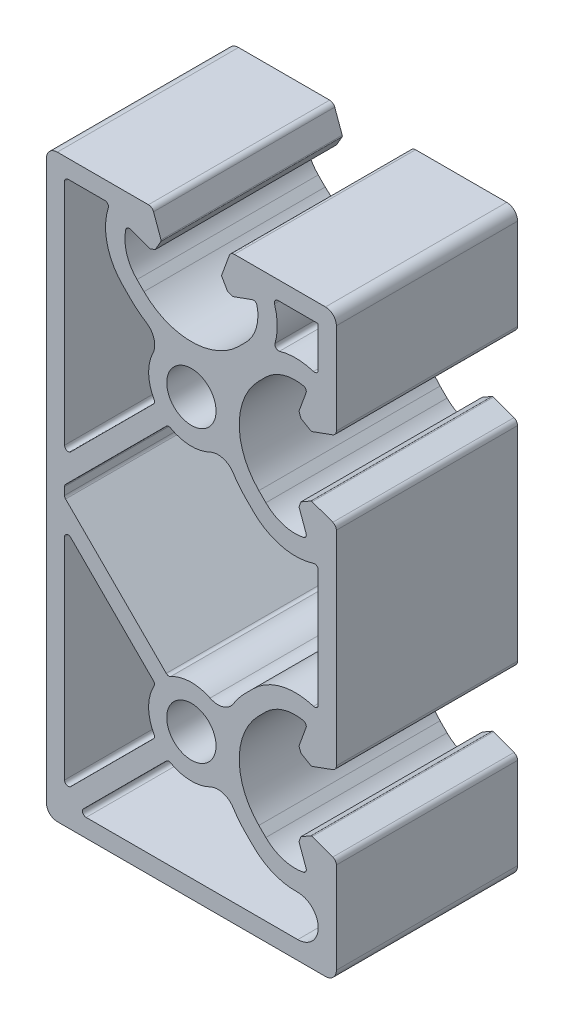
SolidWorks part; units mm, degrees
material "6005-T5"
ref_plane "Front" through (0, 0, 0) normal (0, 0, 1) x (1, 0, 0)
ref_plane "Top" through (0, 0, 0) normal (0, 1, 0) x (1, 0, 0)
ref_plane "Right" through (0, 0, 0) normal (1, 0, 0) x (0, 0, -1)
sketch "Sk Main Extrusion" plane through (0, 0, 0) normal (0, 0, 1) x (1, 0, 0)
  line L118 (-17.5, 37) -> (-17.5, 5.4749)
  line L119 (-16.6464, 5.1213) -> (-5.2369, 16.5309)
  line L120 (-8.3085, 27.4415) -> (-9.4443, 28.5773)
  line L121 (-11.9407, 37.5) -> (-17, 37.5)
  line L122 (-3.4691, 14.7631) -> (-17.3536, 0.8787)
  line L123 (-17.5, 0.5251) -> (-17.5, -0.5251)
  line L124 (-17.3536, -0.8787) -> (-3.4691, -14.7631)
  line L125 (7.4415, -11.6915) -> (8.5773, -10.5557)
  line L126 (17.5, -8.0593) -> (17.5, 8.0593)
  line L127 (8.5773, 10.5557) -> (7.4415, 11.6915)
  line L128 (-17.5, -5.4749) -> (-17.5, -34.5251)
  line L129 (-16.6464, -34.8787) -> (-5.2369, -23.4691)
  line L130 (-5.2369, -16.5309) -> (-16.6464, -5.1213)
  line L131 (-3.4691, -25.2369) -> (-14.8787, -36.6464)
  line L132 (-14.5251, -37.5) -> (14.671, -37.5)
  line L133 (8.5773, -29.4443) -> (7.4415, -28.3085)
  line L134 (17.5, 31.9407) -> (17.5, 37.5)
  line L135 (17.5, 37.5) -> (11.9407, 37.5)
  line L136 (16.6712, -15.8099) -> (19.5065, -14.7779)
  line L137 (20, -14.0732) -> (20, 14.0732)
  line L138 (19.5065, 14.7779) -> (16.6712, 15.8099)
  line L139 (16.4607, 15.7915) -> (15.1113, 15.0124)
  line L140 (15.1113, 15.0124) -> (14.8453, 14.2815)
  line L141 (14.8453, 14.2815) -> (15.8198, 11.6038)
  line L142 (10.2727, 12.4958) -> (9.3093, 13.4593)
  line L143 (9.3093, 26.5407) -> (10.2727, 27.5042)
  line L144 (15.8198, 28.3962) -> (14.8453, 25.7185)
  line L145 (14.8453, 25.7185) -> (15.1113, 24.9876)
  line L146 (15.1113, 24.9876) -> (16.4607, 24.2085)
  line L147 (16.6712, 24.1901) -> (19.5065, 25.2221)
  line L148 (20, 25.9268) -> (20, 38.5)
  line L149 (18.5, 40) -> (5.9268, 40)
  line L150 (5.2221, 39.5065) -> (4.1901, 36.6712)
  line L151 (4.2085, 36.4607) -> (4.9876, 35.1113)
  line L152 (4.9876, 35.1113) -> (5.7185, 34.8453)
  line L153 (5.7185, 34.8453) -> (8.3962, 35.8198)
  line L154 (7.5042, 30.2727) -> (6.5407, 29.3093)
  line L155 (-6.5407, 29.3093) -> (-7.5042, 30.2727)
  line L156 (-8.3962, 35.8198) -> (-5.7185, 34.8453)
  line L157 (-5.7185, 34.8453) -> (-4.9876, 35.1113)
  line L158 (-4.9876, 35.1113) -> (-4.2085, 36.4607)
  line L159 (-4.1901, 36.6712) -> (-5.2221, 39.5065)
  line L160 (-5.9268, 40) -> (-18.5, 40)
  line L161 (-20, 38.5) -> (-20, -38.5)
  line L162 (-18.5, -40) -> (18.5, -40)
  line L163 (20, -38.5) -> (20, -25.9268)
  line L164 (19.5065, -25.2221) -> (16.6712, -24.1901)
  line L165 (16.4607, -24.2085) -> (15.1113, -24.9876)
  line L166 (15.1113, -24.9876) -> (14.8453, -25.7185)
  line L167 (14.8453, -25.7185) -> (15.8198, -28.3962)
  line L168 (10.2727, -27.5042) -> (9.3093, -26.5407)
  line L169 (9.3093, -13.4593) -> (10.2727, -12.4958)
  line L170 (15.8198, -11.6038) -> (14.8453, -14.2815)
  line L171 (14.8453, -14.2815) -> (15.1113, -15.0124)
  line L172 (15.1113, -15.0124) -> (16.4607, -15.7915)
  arc A143 (-17, 37.5) -> (-17.5, 37) centre (-17, 37) ccw
  arc A144 (-17.5, 5.4749) -> (-16.6464, 5.1213) centre (-17, 5.4749) ccw
  arc A145 (-5.2369, 16.5309) -> (-5.1537, 17.1278) centre (-5.5905, 16.8844) ccw
  arc A146 (-5.3076, 22.5767) -> (-5.1537, 17.1278) centre (0, 20) ccw
  arc A147 (-5.3076, 22.5767) -> (-6.2308, 25.7881) centre (-7.5566, 23.6686) ccw
  arc A148 (-8.3085, 27.4415) -> (-6.2308, 25.7881) centre (0, 35.75) ccw
  arc A149 (-11.464, 36.8492) -> (-9.4443, 28.5773) centre (-3.646, 34.3755) ccw
  arc A150 (-11.464, 36.8492) -> (-11.9407, 37.5) centre (-11.9407, 37) ccw
  arc A151 (-2.8722, 14.8463) -> (-3.4691, 14.7631) centre (-3.1156, 14.4095) ccw
  arc A152 (19.5065, -14.7779) -> (20, -14.0732) centre (19.25, -14.0732) ccw
  arc A153 (20, 14.0732) -> (19.5065, 14.7779) centre (19.25, 14.0732) ccw
  arc A154 (16.6712, 15.8099) -> (16.4607, 15.7915) centre (16.5857, 15.575) ccw
  arc A155 (15.4507, 10.943) -> (15.8198, 11.6038) centre (15.35, 11.4328) ccw
  arc A156 (10.2727, 12.4958) -> (15.4507, 10.943) centre (14.3032, 16.5263) ccw
  arc A157 (9.3093, 26.5407) -> (9.3093, 13.4593) centre (15.85, 20) ccw
  arc A158 (15.4507, 29.057) -> (10.2727, 27.5042) centre (14.3032, 23.4737) ccw
  arc A159 (15.8198, 28.3962) -> (15.4507, 29.057) centre (15.35, 28.5672) ccw
  arc A160 (16.4607, 24.2085) -> (16.6712, 24.1901) centre (16.5857, 24.425) ccw
  arc A161 (19.5065, 25.2221) -> (20, 25.9268) centre (19.25, 25.9268) ccw
  arc A162 (20, 38.5) -> (18.5, 40) centre (18.5, 38.5) ccw
  arc A163 (5.9268, 40) -> (5.2221, 39.5065) centre (5.9268, 39.25) ccw
  arc A164 (4.1901, 36.6712) -> (4.2085, 36.4607) centre (4.425, 36.5857) ccw
  arc A165 (9.057, 35.4507) -> (8.3962, 35.8198) centre (8.5672, 35.35) ccw
  arc A166 (7.5042, 30.2727) -> (9.057, 35.4507) centre (3.4737, 34.3032) ccw
  arc A167 (-6.5407, 29.3093) -> (6.5407, 29.3093) centre (0, 35.85) ccw
  arc A168 (-9.057, 35.4507) -> (-7.5042, 30.2727) centre (-3.4737, 34.3032) ccw
  arc A169 (-8.3962, 35.8198) -> (-9.057, 35.4507) centre (-8.5672, 35.35) ccw
  arc A170 (-4.2085, 36.4607) -> (-4.1901, 36.6712) centre (-4.425, 36.5857) ccw
  arc A171 (-5.2221, 39.5065) -> (-5.9268, 40) centre (-5.9268, 39.25) ccw
  arc A172 (-18.5, 40) -> (-20, 38.5) centre (-18.5, 38.5) ccw
  arc A173 (-20, -38.5) -> (-18.5, -40) centre (-18.5, -38.5) ccw
  arc A174 (18.5, -40) -> (20, -38.5) centre (18.5, -38.5) ccw
  arc A175 (20, -25.9268) -> (19.5065, -25.2221) centre (19.25, -25.9268) ccw
  arc A176 (16.6712, -24.1901) -> (16.4607, -24.2085) centre (16.5857, -24.425) ccw
  arc A177 (15.4507, -29.057) -> (15.8198, -28.3962) centre (15.35, -28.5672) ccw
  arc A178 (10.2727, -27.5042) -> (15.4507, -29.057) centre (14.3032, -23.4737) ccw
  arc A179 (9.3093, -13.4593) -> (9.3093, -26.5407) centre (15.85, -20) ccw
  arc A180 (15.4507, -10.943) -> (10.2727, -12.4958) centre (14.3032, -16.5263) ccw
  arc A181 (15.8198, -11.6038) -> (15.4507, -10.943) centre (15.35, -11.4328) ccw
  arc A182 (16.4607, -15.7915) -> (16.6712, -15.8099) centre (16.5857, -15.575) ccw
  arc A183 (-17.3536, 0.8787) -> (-17.5, 0.5251) centre (-17, 0.5251) ccw
  arc A184 (-17.5, -0.5251) -> (-17.3536, -0.8787) centre (-17, -0.5251) ccw
  arc A185 (-3.4691, -14.7631) -> (-2.8722, -14.8463) centre (-3.1156, -14.4095) ccw
  arc A186 (2.5767, -14.6924) -> (-2.8722, -14.8463) centre (0, -20) ccw
  arc A187 (2.5767, -14.6924) -> (5.7881, -13.7692) centre (3.6686, -12.4434) ccw
  arc A188 (7.4415, -11.6915) -> (5.7881, -13.7692) centre (15.75, -20) ccw
  arc A189 (16.8492, -8.536) -> (8.5773, -10.5557) centre (14.3755, -16.354) ccw
  arc A190 (16.8492, -8.536) -> (17.5, -8.0593) centre (17, -8.0593) ccw
  arc A191 (17.5, 8.0593) -> (16.8492, 8.536) centre (17, 8.0593) ccw
  arc A192 (8.5773, 10.5557) -> (16.8492, 8.536) centre (14.3755, 16.354) ccw
  arc A193 (5.7881, 13.7692) -> (7.4415, 11.6915) centre (15.75, 20) ccw
  arc A194 (5.7881, 13.7692) -> (2.5767, 14.6924) centre (3.6686, 12.4434) ccw
  arc A195 (-2.8722, 14.8463) -> (2.5767, 14.6924) centre (0, 20) ccw
  arc A196 (-16.6464, -5.1213) -> (-17.5, -5.4749) centre (-17, -5.4749) ccw
  arc A197 (-17.5, -34.5251) -> (-16.6464, -34.8787) centre (-17, -34.5251) ccw
  arc A198 (-5.2369, -23.4691) -> (-5.1537, -22.8722) centre (-5.5905, -23.1156) ccw
  arc A199 (-5.1537, -17.1278) -> (-5.1537, -22.8722) centre (0, -20) ccw
  arc A200 (-5.1537, -17.1278) -> (-5.2369, -16.5309) centre (-5.5905, -16.8844) ccw
  arc A201 (-2.8722, -25.1537) -> (-3.4691, -25.2369) centre (-3.1156, -25.5905) ccw
  arc A202 (-14.8787, -36.6464) -> (-14.5251, -37.5) centre (-14.5251, -37) ccw
  arc A203 (14.671, -37.5) -> (14.5952, -31.8431) centre (14.671, -34.671) ccw
  arc A204 (8.5773, -29.4443) -> (14.5952, -31.8431) centre (14.3755, -23.646) ccw
  arc A205 (5.7881, -26.2308) -> (7.4415, -28.3085) centre (15.75, -20) ccw
  arc A206 (5.7881, -26.2308) -> (2.5767, -25.3076) centre (3.6686, -27.5566) ccw
  arc A207 (-2.8722, -25.1537) -> (2.5767, -25.3076) centre (0, -20) ccw
  arc A208 (16.8492, 31.464) -> (17.5, 31.9407) centre (17, 31.9407) ccw
  arc A209 (16.8492, 31.464) -> (12.1568, 31.5401) centre (14.3755, 23.646) ccw
  arc A210 (11.5401, 32.1568) -> (12.1568, 31.5401) centre (12.0215, 32.0215) ccw
  arc A211 (11.5401, 32.1568) -> (11.464, 36.8492) centre (3.646, 34.3755) ccw
  arc A212 (11.9407, 37.5) -> (11.464, 36.8492) centre (11.9407, 37) ccw
  circle A213 centre (0, -20) radius 3.4
  circle A214 centre (0, 20) radius 3.4
  point P181 (0, 0)
extrude "Main Extrusion" add sketch "Sk Main Extrusion" against normal blind 25
sketch "Threaded Insert Mate Sketch" plane through (0, 0, 0) normal (0, 0, 1) x (1, 0, 0)
  line L0 (17.5, 0) -> (-17.5, 0) construction
  line L3 (17.5, -8.0593) -> (17.5, 8.0593) construction
  line L4 (-17.5, 0.5251) -> (-17.5, -0.5251) construction
  circle A0 centre (0, 32.7) radius 5.6515
  circle A2 centre (12.7, 20) radius 5.6515
  circle A3 centre (0, 7.3) radius 5.6515
  circle A4 centre (-12.7, 20) radius 5.6515
  circle A5 centre (12.7, -20) radius 5.6515
  circle A6 centre (0, 20) radius 3.4 construction
  point P14 (0, 20)
  dimension "D2" = 11.303
  dimension "D1" = 12.7
  dimension "D3" = 4
equation "\"Weight kg\"= round ( \"SW-Mass\" , 2 )"
equation "\"Weight lbs\"= round ( \"SW-Mass\" * 2.2046 , 2 )"
equation "\"Length mm\"= round ( \"Length@Main Extrusion\" , 2 )"
equation "\"Length in\"= round ( \"Length@Main Extrusion\" / 25.4 , 3 )"
